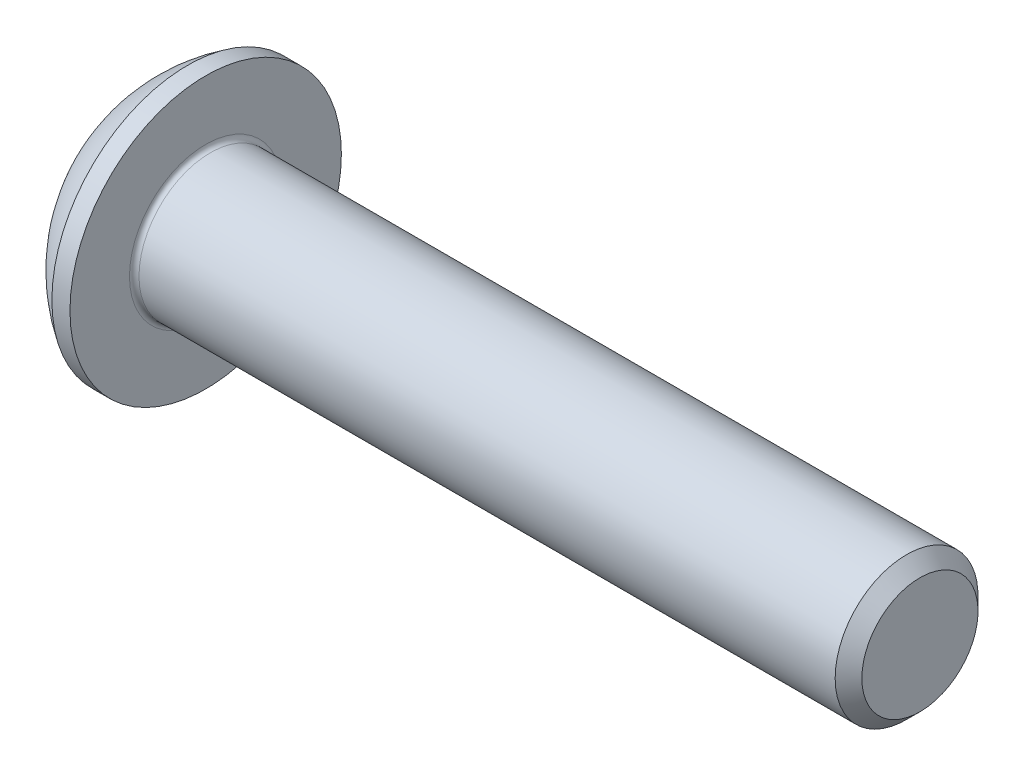
SolidWorks part; units mm, degrees
ref_plane "Plane1" through (0, 0, 0) normal (0, 0, 1) x (1, 0, 0)
ref_plane "Plane2" through (0, 0, 0) normal (0, 1, 0) x (1, 0, 0)
ref_plane "Plane3" through (0, 0, 0) normal (1, 0, 0) x (0, 0, -1)
sketch "BodySke" plane through (0, 0, 0) normal (0, 0, 1) x (1, 0, 0)
  line L0 (16.65, 0) -> (16.65, 1.2195)
  line L1 (16.3695, 1.5) -> (1.65, 1.5)
  line L2 (1.65, 1.5) -> (1.65, 2.85)
  line L3 (1.65, 2.85) -> (1.27, 2.85)
  line L4 (0, 0) -> (101.6, 0) construction
  line L5 (1.65, -2.85) -> (1.27, -2.85) construction
  line L6 (55.6768, -1.5) -> (1.65, -1.5) construction
  line L7 (16.65, 0) -> (0, 0)
  line L8 (0, 1.425) -> (0, -1.425) construction
  line L9 (0, 0) -> (0, 1.425)
  line L10 (16.65, 1.2195) -> (16.3695, 1.5)
  line L11 (16.65, -1.2195) -> (16.3695, -1.5) construction
  line L12 (2.15, 9.525) -> (2.15, -1.5) construction
  line L13 (4.65, 9.525) -> (4.65, -1.5) construction
  arc A1 (0, 1.425) -> (1.27, 2.85) centre (3.0334, 0) cw
  dimension "D1" = 2.85
  dimension "Diameter" = 3
  dimension "Length" = 15
  dimension "Head_dia" = 5.7
  dimension "Head_ht" = 1.65
  dimension "Head_side_ht" = 0.38
  dimension "Minor_dia" = 2.439
  dimension "Body_ch_ang" = 45
  dimension "Advance" = 0.5
  dimension "Thread_nom" = 12
revolve "BaseBody" add sketch "BodySke" angle 360 about L4
cosmetic thread "ThreadCosmetic" [suppressed] parameters "Thread_length"=12, "Thread_minor"=2.439
fillet "Fillet1" radius 0.1 1 edges at (1.65, 0, 1.5)
sketch "Sketch2" plane through (0, 0, 0) normal (0, 0, 1) x (1, 0, 0)
  line L0 (0, 1) -> (1.04, 1)
  line L1 (1.04, 1) -> (1.6174, 0)
  line L3 (1.6174, 0) -> (0, 0)
  line L4 (0, 0) -> (0, 1)
  line L5 (0, -1) -> (1.04, -1) construction
  line L6 (0, 0) -> (47.625, 0) construction
  dimension "D2" = 60
  dimension "PreBroach_depth" = 1.04
  dimension "PreBroach_dia" = 2
revolve "PreBroach" cut sketch "Sketch2" angle 360 about L6
sketch "Sketch3" plane through (0, 0, 0) normal (1, 0, 0) x (0, 0, -1)
  line L0 (-1, -0.5774) -> (-1, 0.5774)
  line L1 (-1, 0.5774) -> (0, 1.1547)
  line L2 (0, 1.1547) -> (1, 0.5774)
  line L3 (1, 0.5774) -> (1, -0.5774)
  line L4 (1, -0.5774) -> (0, -1.1547)
  line L5 (0, -1.1547) -> (-1, -0.5774)
  dimension "D1" = 1
  dimension "D2" = 1
  dimension "D3" = 2
  dimension "Hex_size" = 2
extrude "Hex" cut sketch "Sketch3" along normal blind 1.04
sketch "ThdSchSke" plane through (0, 0, 0) normal (0, 0, 1) x (1, 0, 0)
  line L0 (4.65, -1.2195) -> (4.4536, -1.5)
  line L1 (4.65, -1.2195) -> (4.8464, -1.5)
  line L2 (4.8464, -1.5) -> (4.8464, -1.875)
  line L3 (-3.175, 0) -> (5.1513, 0) construction
  line L5 (4.8464, -1.875) -> (4.4536, -1.875)
  line L6 (4.4536, -1.875) -> (4.4536, -1.5)
  dimension "Thread_minor" = 2.439
  dimension "Diameter" = 3
  dimension "Start" = 4.65
  dimension "SideAngle" = 55
  dimension "VeeAngle" = 70
  dimension "Overcut" = 3.75
revolve "ThreadSchematic" [suppressed] cut sketch "ThdSchSke" angle 360 about L3
pattern_linear "ThdSchPat" [suppressed]
equation "\"D1@BodySke\" = \"Head_dia@BodySke\" * .5"
equation "\"Thread_minor@ThreadCosmetic\" = \"Minor_dia@BodySke\""
equation "\"D1@Sketch3\" = \"Hex_size@Sketch3\" / 2"
equation "\"D2@Sketch3\" = \"D1@Sketch3\""
equation "\"D3@Sketch3\" = \"Hex_size@Sketch3\""
equation "\"Thread_length@ThreadCosmetic\" = ((sgn( (\"Length@BodySke\" - \"Advance@BodySke\" * 2.0) - \"Thread_nom@BodySke\" )-1)*( (\"Length@BodySke\" - \"Advance@BodySke\" * 2.0) - \"Thread_nom@BodySke\" ))/-2+ \"Thread_nom@BodySke\""
equation "\"Thread_minor@ThdSchSke\" = \"Minor_dia@BodySke\""
equation "\"Diameter@ThdSchSke\" = \"Diameter@BodySke\""
equation "\"Overcut@ThdSchSke\" = \"Diameter@BodySke\" * 1.25"
equation "\"Start@ThdSchSke\" = \"Head_ht@BodySke\" + \"Length@BodySke\" - \"Thread_length@ThreadCosmetic\"  '---Non-countersunk---"
equation "\"Num_threads@ThdSchPat\" = int( \"Thread_length@ThreadCosmetic\" / \"Advance@BodySke\" + 0.999 )  + 1"
equation "\"Advance@ThdSchPat\" = \"Thread_length@ThreadCosmetic\" /  (\"Num_threads@ThdSchPat\" - 1) 'relax it"
equation "\"Num_threads@ThdSchPat\" = \"Num_threads@ThdSchPat\" - sgn( \"Num_threads@ThdSchPat\" - 1) '---chamfered tips only---"
